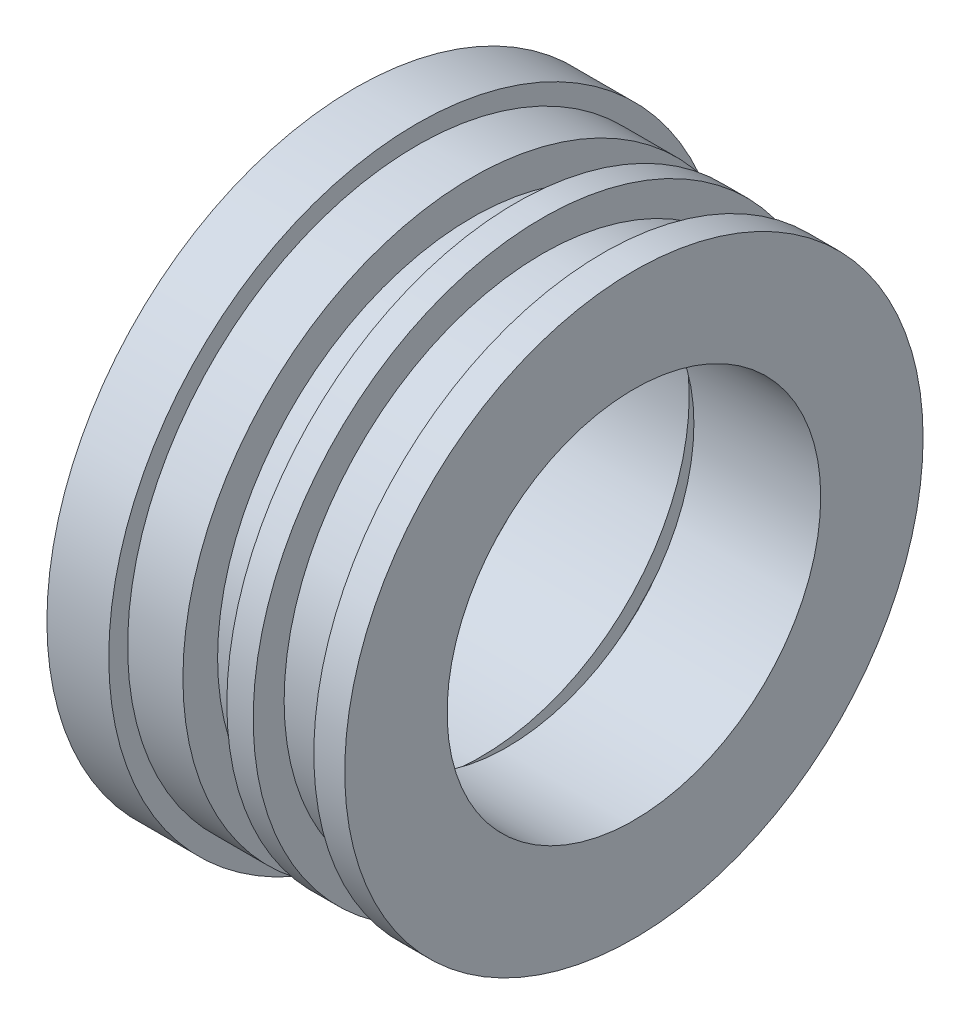
SolidWorks part; units mm, degrees
ref_plane "Front Plane" through (0, 0, 0) normal (0, 0, 1) x (1, 0, 0)
ref_plane "Top Plane" through (0, 0, 0) normal (0, 1, 0) x (1, 0, 0)
ref_plane "Right Plane" through (0, 0, 0) normal (1, 0, 0) x (0, 0, -1)
sketch "Sketch1" plane through (0, 0, 0) normal (0, 0, 1) x (1, 0, 0)
  line L0 (-6.2484, 12.6492) -> (-6.2484, 8.5508)
  line L4 (-3.7084, 11.8745) -> (-3.7084, 12.6492)
  line L5 (-3.7084, 12.6492) -> (-6.2484, 12.6492)
  line L31 (0, 0) -> (-7.2739, 0) construction
  line L34 (0, 0) -> (0, 8.5508) construction
  line L35 (0, 8.5508) -> (0, 7.6708)
  line L36 (0, 7.6708) -> (5.207, 7.6708)
  line L37 (5.207, 7.6708) -> (5.207, 11.8745)
  line L38 (-3.7084, 11.8745) -> (1.4478, 11.8745)
  line L39 (1.4478, 11.8745) -> (1.4478, 10.6045)
  line L40 (1.4478, 10.6045) -> (3.937, 10.6045)
  line L41 (3.937, 10.6045) -> (3.937, 11.8745)
  line L42 (3.937, 11.8745) -> (5.207, 11.8745)
  line L43 (-6.2484, 8.5508) -> (-1.0733, 8.5508)
  line L44 (-1.0733, 8.5508) -> (-1.0733, 9.1715)
  line L45 (-1.0733, 9.1715) -> (0, 9.1715)
  line L46 (0, 9.1715) -> (0, 8.5508)
  dimension "D6" = 12.6492
  dimension "D8" = 2.54
  dimension "D2" = 7.6708
  dimension "D3" = 6.2484
  dimension "D4" = 1.27
  dimension "D5" = 2.4892
  dimension "D7" = 11.8745
  dimension "D9" = 1.27
  dimension "D1" = 5.207
  dimension "D10" = 8.5508
revolve "Revolve1" add sketch "Sketch1" angle 360 about L31
ref_plane "Plane1" through (-0.5367, 0, 0) normal (-1, 0, 0) x (0, 0, 1)
ref_plane "Plane2" through (0, 11.8745, 0) normal (0, 1, 0) x (1, 0, 0)
sketch "Sketch2" plane through (0, 11.8745, 0) normal (0, 1, 0) x (1, 0, 0)
  line L0 (-0.5367, 10.0886) -> (-0.5367, -10.0886) construction
  point P0 (-0.5367, 0)
hole_wizard "1/32 (0.03125) Diameter Hole1" positions "Sketch2" profile "Sketch3" hole size "1/32" standard "ANSI Inch"
sketch "Sketch3" plane through (-0.5367, 11.8745, 0) normal (1, 0, 0) x (0, 0, 1)
  line L0 (0, 0) -> (0, 2.703)
  line L1 (0, 2.703) -> (0.3969, 2.703)
  line L2 (0.3969, 2.703) -> (0.3969, 0)
  line L5 (0.3969, 0) -> (0, 0)
  line L11 (0, -6.35) -> (0, 107.95) construction
  dimension "Thru Hole Dia." = 0.7937
  dimension "Thru Hole Depth" = 2.703
sketch "Sketch4" plane through (0, 0, 0) normal (0, 0, 1) x (1, 0, 0)
  line L0 (-0.1398, 11.8745) -> (0.365, 11.8745)
  line L1 (-0.9335, 11.8745) -> (-1.4383, 11.8745)
  line L4 (-1.4383, 11.8745) -> (-1.4383, 10.4504)
  line L5 (-1.4383, 10.4504) -> (0.365, 10.4504)
  line L6 (0.365, 10.4504) -> (0.365, 11.8745)
  spline S0 degree 2 poles (-0.1398, 11.8745) (-0.5367, 11.8612) (-0.9335, 11.8745) knots 0 0 0 1 1 1 weights 0.011478 0.011874 0.012271 construction
  spline S1 degree 2 poles (-0.1398, 11.8745) (-0.5367, 11.8612) (-0.9335, 11.8745) knots 0 0 0 1 1 1 weights 0.011478 0.011874 0.012271
ref_axis "Axis2" through (-6.8212, 0, 0) along (1, 0, 0)
revolve "Cut-Revolve3" cut sketch "Sketch4" angle 360 about axis through (-6.8212, 0, 0) along (1, 0, 0)
equation "\"Cavity_Depth\" = 0.031in"
equation "\"Cavity_Width\" = 0.031in"
equation "\"Tooth_Width\" = .01in"
equation "\"Shaft_Seal_OD\"= 17mm'diameter at seal area"
equation "\"Shaft_clearance\"= .002in"
equation "\"O-Ring_ID\"= .801in"
equation "\"O-Ring_CS\"= .070in"
equation "\"Shaft_OD\"= .5in"
equation "\"Flange_OD\"=2.3in"
equation "\"seal2dia\"=0.3in"
equation "\"after_laby_len\"=0.75in"
equation "\"D2@Sketch1\"=\"seal2dia\"+\"Shaft_clearance\""
equation "\"D3@Sketch1\"=\"Cavity_Width\"*6+\"Tooth_Width\"*6"
equation "\"D1@Sketch1\"=\"Cavity_Width\"*5+5*\"Tooth_Width\""
equation "\"D10@Sketch1\"=\"Shaft_Seal_OD\"/2+\"Shaft_clearance\""
